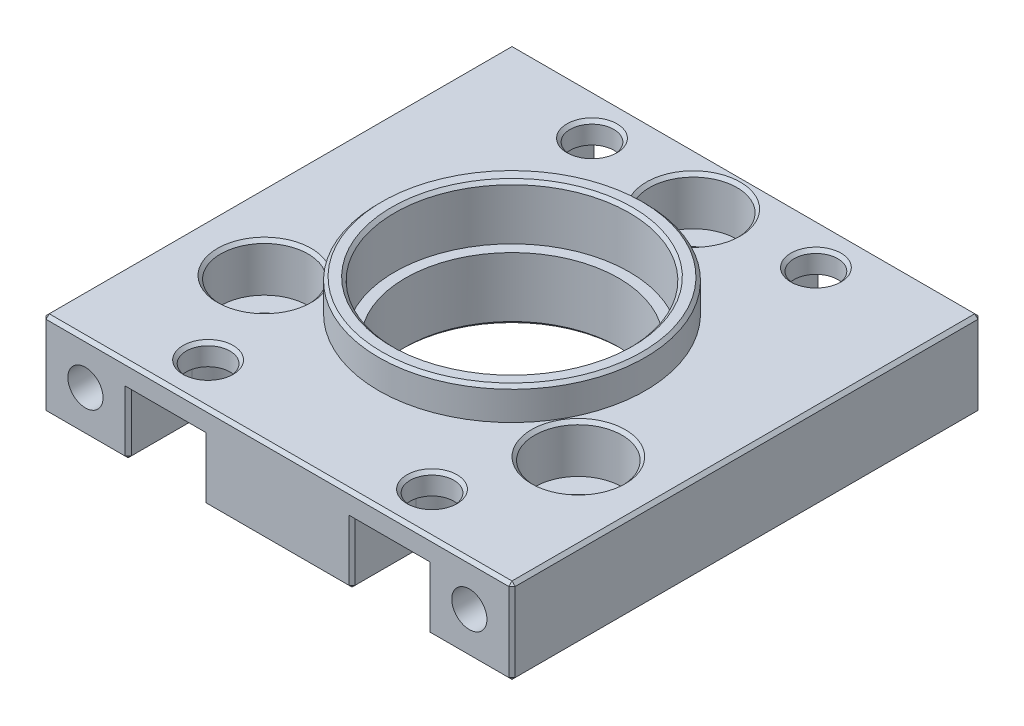
SolidWorks part; units mm, degrees
ref_plane "Front Plane" through (0, 0, 0) normal (0, 0, 1) x (1, 0, 0)
ref_plane "Top Plane" through (0, 0, 0) normal (0, 1, 0) x (1, 0, 0)
ref_plane "Right Plane" through (0, 0, 0) normal (1, 0, 0) x (0, 0, -1)
sketch "Sketch1" plane through (0, 0, 0) normal (0, 1, 0) x (1, 0, 0)
  line L0 (0, 0) -> (0, 22) construction
  line L1 (-22, -22) -> (22, -22)
  line L2 (-22, -22) -> (-22, 22)
  line L3 (-22, 22) -> (22, 22)
  line L4 (22, -22) -> (22, 22)
  line L5 (-22, -22) -> (22, 22) construction
  line L6 (-22, 22) -> (22, -22) construction
  line L7 (0, 17) -> (0, 0) construction
  circle A0 centre (0, 0) radius 17 construction
  circle A1 centre (0, 17) radius 2.05
  circle A2 centre (0, 0) radius 17 construction
  circle A3 centre (14.7224, -8.5) radius 2.05
  circle A4 centre (0, 0) radius 17 construction
  circle A5 centre (-14.7224, -8.5) radius 2.05
  circle A6 centre (0, 0) radius 10
  point P0 (0, 0)
  point P20 (0, 0)
  dimension "D2" = 34
  dimension "D3" = 4.1
  dimension "D5" = 20
  dimension "D1" = 44
  dimension "D4" = 3
extrude "Boss-Extrude1" add sketch "Sketch1" along normal mid plane 11
sketch "Sketch3" plane through (0, 5.5, 0) normal (0, 1, 0) x (1, 0, 0)
  circle A0 centre (0, 0) radius 11
  dimension "D1" = 22
extrude "Cut-Extrude1" cut sketch "Sketch3" against normal blind 5.1
sketch "Sketch4" plane through (0, 0, -22) normal (0, 0, -1) x (-1, 0, 0)
  line L0 (18, -1.5) -> (-18, -1.5)
  line L1 (-22, 5.5) -> (22, 5.5) construction
  line L2 (-22, 5.5) -> (-22, -5.5) construction
  line L3 (-22, -5.5) -> (22, -5.5) construction
  point P3 (0, -1.5)
  dimension "D1" = 4
  dimension "D2" = 4
hole_wizard "M4x0.7 Tapped Hole1" positions "3DSketch1" profile "Sketch5" tap size "M4x0.7" standard "ANSI Metric"
sketch3d "3DSketch1"
  point P0 (-18, -1.5, -22)
  point P3 (18, -1.5, -22)
sketch "Sketch5" plane through (-18, -1.5, -22) normal (1, 0, 0) x (0, 1, 0)
  line L0 (0, 0) -> (0, 7.9914)
  line L1 (0, 7.9914) -> (1.65, 7)
  line L2 (1.65, 7) -> (1.65, 0)
  line L5 (1.65, 0) -> (0, 0)
  line L10 (0, 7.9914) -> (-1.65, 7) construction
  line L11 (0, -6.35) -> (0, 107.95) construction
  dimension "Tap Drill Dia." = 3.3
  dimension "Tap Drill Depth" = 7
  dimension "Drill Angle" = 118
cosmetic thread "Hole Thread1" parameters "D1"=7, "D2"=4
cosmetic thread "Hole Thread2" parameters "D1"=7, "D2"=4
mirror "Mirror1" about plane through (0, 0, 0) normal (0, 0, 1) of "M4x0.7 Tapped Hole1"
cosmetic thread "Hole Thread3" parameters "D1"=7, "D2"=4
cosmetic thread "Hole Thread4" parameters "D1"=7, "D2"=4
sketch "Sketch6" plane through (0, 5.5, 0) normal (0, 1, 0) x (1, 0, 0)
  line L0 (0, -24.2) -> (0, 24.2) construction
  line L1 (-22, 22) -> (-14, 22)
  line L2 (-22, 22) -> (-22, 10)
  line L3 (-22, 10) -> (-14, 10)
  line L4 (-14, 22) -> (-14, 10)
  line L5 (-22, 22) -> (-14, 10) construction
  line L6 (-22, 10) -> (-14, 22) construction
  line L7 (22, 22) -> (14, 22)
  line L8 (22, 22) -> (22, 10)
  line L9 (22, 10) -> (14, 10)
  line L10 (14, 22) -> (14, 10)
  line L11 (-24.2, 0) -> (24.2, 0) construction
  line L12 (22, -10) -> (14, -10) construction
  line L13 (14, -22) -> (14, -10) construction
  line L14 (-22, -10) -> (-14, -10) construction
  line L15 (-14, -22) -> (-14, -10) construction
  line L16 (-22, -22) -> (22, -22) construction
  line L17 (-22, -22) -> (22, -22)
  line L29 (-20, 22) -> (-20, -22)
  line L30 (-20, 22) -> (-20, -22)
  line L32 (20, -22) -> (20, 22)
  line L33 (20, -22) -> (20, 22)
  line L36 (22, 20) -> (-22, 20)
  line L37 (22, 20) -> (-22, 20)
  circle A1 centre (-14.7224, -8.5) radius 4.1
  circle A2 centre (0, 0) radius 13
  circle A3 centre (0, 0) radius 13 construction
  circle A7 centre (0, 17) radius 4.1
  circle A8 centre (14.7224, -8.5) radius 4.1
  point P7 (-18, 16)
  point P38 (0, 0)
  circle M18 centre (0, 17) radius 2.05
  circle M19 centre (14.7224, -8.5) radius 2.05
  circle M20 centre (-14.7224, -8.5) radius 2.05
  dimension "D8" = 8.2
  dimension "D2" = 8
  dimension "D3" = 12
  dimension "D1" = 2
  dimension "D4" = 2
  dimension "D5" = 2
  dimension "D6" = 2
  dimension "D7" = 3
extrude "Cut-Extrude2" cut sketch "Sketch6" against normal blind 7.5 contours A1 M20 | A8 M19 | A7 L37 M18 | L37 A7
sketch "Sketch7" plane through (0, 5.5, 0) normal (0, 1, 0) x (1, 0, 0)
  circle A2 centre (0, 0) radius 12.5
  circle A3 centre (0, 0) radius 12.5
  circle M2 centre (-14.7224, -8.5) radius 4.1
  circle M3 centre (14.7224, -8.5) radius 4.1
  circle M4 centre (0, 17) radius 4.1
  line M6 (22, -22) -> (22, 22)
  line M7 (22, 22) -> (-22, 22)
  line M8 (-22, 22) -> (-22, -22)
  line M9 (-22, -22) -> (22, -22)
  dimension "D1" = 1.5
extrude "Cut-Extrude3" cut sketch "Sketch7" against normal blind 3 contours A3 M9 M6 M7 M8 M3 M4 M2
sketch "Sketch8" plane through (0, 2.5, 0) normal (0, 1, 0) x (1, 0, 0)
  line L0 (-14, -22) -> (-14, -10) construction
  line L1 (-22, -10) -> (-14, -10) construction
  line L2 (-14, -22) -> (-14, -10)
  line L3 (-22, -10) -> (-14, -10)
  line L5 (0, -6.05) -> (0, 6.05) construction
  line L6 (14, -22) -> (14, -10)
  line L7 (22, -10) -> (14, -10)
  line L8 (-22, 22) -> (22, 22) construction
  line L9 (-14, 22) -> (-14, 10) construction
  line L10 (-22, 22) -> (22, 22)
  line L11 (-14, 22) -> (-14, 10)
  line L12 (-5, 22) -> (-5, 12.886)
  line L13 (5, 22) -> (5, 12.886)
  line L14 (14, 22) -> (14, 10)
  circle A0 centre (-14.7224, -8.5) radius 5
  arc A1 (-6.0718, -12.0575) -> (-14, -16.9417) centre (-8.5314, -16.9417) ccw
  circle A2 centre (0, 0) radius 12.5 construction
  circle A3 centre (0, 0) radius 12.5
  circle A4 centre (0, 0) radius 13.5
  arc A6 (6.0718, -12.0575) -> (14, -16.9417) centre (8.5314, -16.9417) cw
  arc A7 (-14, 17.5) -> (-5, 17.5) centre (-9.5, 17.5) ccw
  arc A8 (14, 17.5) -> (5, 17.5) centre (9.5, 17.5) cw
  dimension "D1" = 10
  dimension "D2" = 27
  dimension "D3" = 5
sketch "草图1" plane through (0, -5.5, 0) normal (0, -1, 0) x (1, 0, 0)
  line L0 (10.5, -36) -> (10.5, -16) construction
  line L1 (7, -36) -> (7, -16)
  line L2 (14, -36) -> (14, -16)
  line L3 (22, 22) -> (22, -22) construction
  line L4 (22, -22) -> (-22, -22) construction
  line L5 (0, 0) -> (35.0725, 0) construction
  line L6 (0, 0) -> (0, -50.2457) construction
  line L7 (-10.5, -36) -> (-10.5, -16) construction
  line L8 (-7, -36) -> (-7, -16)
  line L9 (-14, -36) -> (-14, -16)
  line L10 (-10.5, 36) -> (-10.5, 16) construction
  line L11 (-7, 36) -> (-7, 16)
  line L12 (-14, 36) -> (-14, 16)
  line L13 (10.5, 36) -> (10.5, 16) construction
  line L14 (7, 36) -> (7, 16)
  line L15 (14, 36) -> (14, 16)
  arc A0 (7, -36) -> (14, -36) centre (10.5, -36) ccw
  arc A1 (14, -16) -> (7, -16) centre (10.5, -16) ccw
  arc A2 (-7, -36) -> (-14, -36) centre (-10.5, -36) cw
  arc A3 (-14, -16) -> (-7, -16) centre (-10.5, -16) cw
  arc A4 (-7, 36) -> (-14, 36) centre (-10.5, 36) ccw
  arc A5 (-14, 16) -> (-7, 16) centre (-10.5, 16) ccw
  arc A6 (7, 36) -> (14, 36) centre (10.5, 36) cw
  arc A7 (14, 16) -> (7, 16) centre (10.5, 16) cw
  point P2 (10.5, -26)
  point P17 (-10.5, -26)
  point P24 (-10.5, 26)
  point P31 (10.5, 26)
  dimension "D4" = 6
  dimension "D1" = 7
  dimension "D2" = 20
  dimension "D3" = 8
extrude "切除-拉伸1" cut sketch "草图1" against normal blind 6
sketch "草图2" plane through (0, 0.5, 0) normal (0, -1, 0) x (1, 0, 0)
  line L0 (0, 0) -> (0, 28.755) construction
  line L1 (0, 0) -> (30.6816, 0) construction
  line L2 (7, 22) -> (14, 22) construction
  line L3 (7, 22) -> (7, 16) construction
  circle A0 centre (10.5, 18) radius 2.05
  circle A1 centre (-10.5, 18) radius 2.05
  circle A2 centre (-10.5, -18) radius 2.05
  circle A3 centre (10.5, -18) radius 2.05
  dimension "D1" = 4.1
  dimension "D2" = 4
  dimension "D3" = 3.5
extrude "切除-拉伸2" cut sketch "草图2" against normal blind 5
chamfer "倒角1" distance 0.3 angle 45 49 edges at (-14.7224, -5.5, 10.55) (0, -5.5, -14.95) (0, -5.5, 10) (14.7224, -5.5, 10.55) (0, 2.5, -12.9) (-14.7224, 2.5, 12.6) (14.7224, 2.5, 12.6) (18, -5.5, 22) (22, -5.5, 0) (18, -5.5, -22) (14, -2.5, -22) (14, -5.5, -19) (10.5, -5.5, -12.5) (7, -5.5, -19) (7, -2.5, -22) (0, -5.5, -22) (-7, -2.5, -22) (-7, -5.5, -19) (-10.5, -5.5, -12.5) (-14, -5.5, -19) (-14, -2.5, -22) (-18, -5.5, -22) (-22, -5.5, 0) (14, -2.5, 22) (14, -5.5, 19) (10.5, -5.5, 12.5) (7, -5.5, 19) (7, -2.5, 22) (0, -5.5, 22) (-7, -2.5, 22) (-7, -5.5, 19) (-10.5, -5.5, 12.5) (-14, -5.5, 19) (-14, -2.5, 22) (-18, -5.5, 22) (-22, -1.5, 22) (-22, 2.5, 0) (0, 2.5, 22) (22, 2.5, 0) (0, 2.5, -22) (0, 5.5, 11) (0, 5.5, 12.5) (22, -1.5, 22) (22, -1.5, -22) (-22, -1.5, -22) (10.5, 2.5, -15.95) (-10.5, 2.5, -15.95) (10.5, 2.5, 20.05) (-10.5, 2.5, 20.05)
